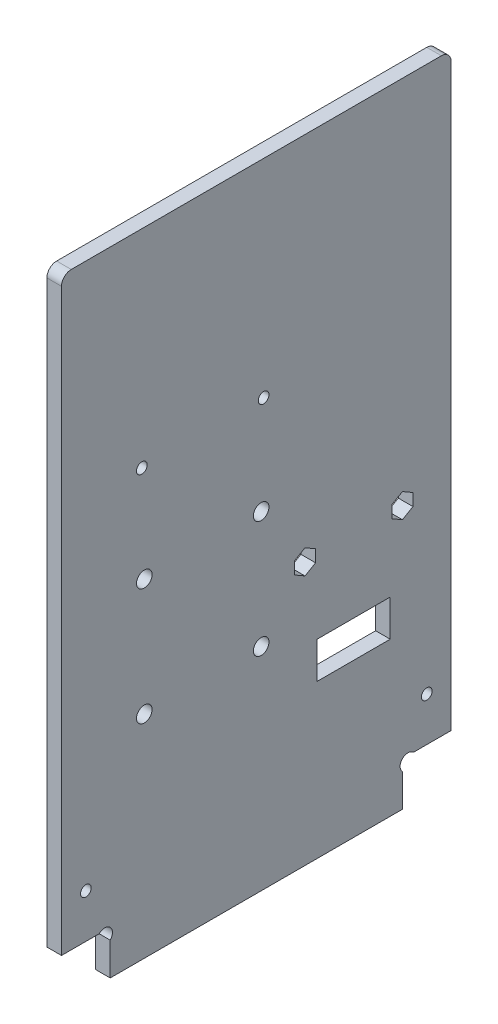
SolidWorks part; units mm, degrees
ref_plane "Plan de face" through (0, 0, 0) normal (0, 0, 1) x (1, 0, 0)
ref_plane "Plan de dessus" through (0, 0, 0) normal (0, 1, 0) x (1, 0, 0)
ref_plane "Plan de droite" through (0, 0, 0) normal (1, 0, 0) x (0, 0, -1)
sketch "Esquisse1" plane through (0, 0, 0) normal (1, 0, 0) x (0, 0, -1)
  line L8 (10, 6.7373) -> (10, 0)
  line L9 (70, 6.7373) -> (70, 0)
  line L10 (7.7373, 9) -> (0, 9)
  line L11 (10, 0) -> (70, 0)
  line L12 (72.2627, 9) -> (80, 9)
  line L13 (0, 9) -> (0, 130)
  line L14 (0, 130) -> (80, 130)
  line L15 (80, 130) -> (80, 9)
  arc A0 (10, 6.7373) -> (7.7373, 9) centre (8.8686, 7.8686) ccw
  arc A1 (70, 6.7373) -> (72.2627, 9) centre (71.1314, 7.8686) cw
  dimension "D7" = 1.1314
  dimension "D6" = 1.6
  dimension "D1" = 9
  dimension "D2" = 10
  dimension "D3" = 10
  dimension "D4" = 80
  dimension "D5" = 130
  dimension "D8" = 1.1314
  dimension "D9" = 1.1314
  dimension "D10" = 1.1314
extrude "Extrusion1" add sketch "Esquisse1" along normal blind 3
sketch "Esquisse2" plane through (3, 0, 0) normal (1, 0, 0) x (0, 0, -1)
  line L0 (0, 9) -> (7.7373, 9) construction
  line L1 (0, 130) -> (0, 9) construction
  line L2 (80, 9) -> (80, 130) construction
  line L3 (72.2627, 9) -> (80, 9) construction
  circle A4 centre (17, 67.45) radius 1.6
  circle A5 centre (17, 43.45) radius 1.6
  circle A6 centre (41, 43.45) radius 1.6
  circle A7 centre (41, 67.45) radius 1.6
  circle A9 centre (70, 54) radius 1.1
  circle A10 centre (50, 54) radius 1.1
  dimension "D5" = 17
  dimension "D4" = 3.2
  dimension "D6" = 2.2
  dimension "D1" = 58.45
  dimension "D2" = 24
  dimension "D3" = 24
  dimension "D15" = 10
  dimension "D16" = 20
  dimension "D17" = 45
extrude "Enlèv. mat.-Extru.1" cut sketch "Esquisse2" against normal through all
sketch "Esquisse3" plane through (0, 0, 0) normal (-1, 0, 0) x (0, 0, 1)
  line L1 (-67.5, 39) -> (-52.5, 39)
  line L2 (-67.5, 39) -> (-67.5, 31.5)
  line L3 (-67.5, 31.5) -> (-52.5, 31.5)
  line L4 (-52.5, 39) -> (-52.5, 31.5)
  circle A0 centre (-70, 54) radius 1.1 construction
  circle A1 centre (-50, 54) radius 1.1 construction
  dimension "D4" = 2.5
  dimension "D1" = 15
  dimension "D2" = 7.5
  dimension "D3" = 15
  dimension "D5" = 2.5
extrude "Enlèv. mat.-Extru.2" cut sketch "Esquisse3" against normal through all
sketch "Esquisse4" plane through (3, 0, 0) normal (1, 0, 0) x (0, 0, -1)
  line L3 (0, 9) -> (7.7373, 9) construction
  line L4 (0, 130) -> (0, 9) construction
  line L5 (80, 9) -> (80, 130) construction
  circle A2 centre (75, 18) radius 1.1
  circle A3 centre (5, 18) radius 1.1
  dimension "D1" = 2.2
  dimension "D2" = 5
  dimension "D3" = 5
  dimension "D5" = 9
extrude "Enlèv. mat.-Extru.3" cut sketch "Esquisse4" against normal through all
sketch "Esquisse5" plane through (3, 0, 0) normal (1, 0, 0) x (0, 0, -1)
  line L0 (80, 9) -> (80, 130) construction
  line L1 (50, 51.5) -> (52.1651, 52.75)
  line L2 (52.1651, 52.75) -> (52.1651, 55.25)
  line L3 (52.1651, 55.25) -> (50, 56.5)
  line L4 (50, 56.5) -> (47.8349, 55.25)
  line L5 (47.8349, 55.25) -> (47.8349, 52.75)
  line L6 (47.8349, 52.75) -> (50, 51.5)
  line L7 (70, 51.5) -> (72.1651, 52.75)
  line L8 (72.1651, 52.75) -> (72.1651, 55.25)
  line L9 (72.1651, 55.25) -> (70, 56.5)
  line L10 (70, 56.5) -> (67.8349, 55.25)
  line L11 (67.8349, 55.25) -> (67.8349, 52.75)
  line L12 (67.8349, 52.75) -> (70, 51.5)
  circle A0 centre (50, 54) radius 2.1651 construction
  circle A1 centre (70, 54) radius 2.1651 construction
  dimension "D1" = 2.5
  dimension "D2" = 2.5
extrude "Enlèv. mat.-Extru.4" cut sketch "Esquisse5" against normal through all
fillet "Congé1" radius 2 2 edges at (1.5, 130, -80) (1.5, 130, 0)
sketch "Esquisse6" plane through (3, 0, 0) normal (1, 0, 0) x (0, 0, -1)
  line L0 (17, 43.45) -> (17, 35.9367) construction
  line L1 (41, 43.45) -> (41, 36.8364) construction
  circle A0 centre (16.5, 87.45) radius 1.1
  circle A1 centre (41.5, 87.45) radius 1.1
  circle A2 centre (17, 67.45) radius 1.6 construction
  point P4 (41, 74.0651)
  dimension "D1" = 2.2
  dimension "D4" = 24
  dimension "D2" = 0.5
  dimension "D3" = 20
  dimension "D5" = 0.5
extrude "Enlèv. mat.-Extru.5" cut sketch "Esquisse6" against normal through all
